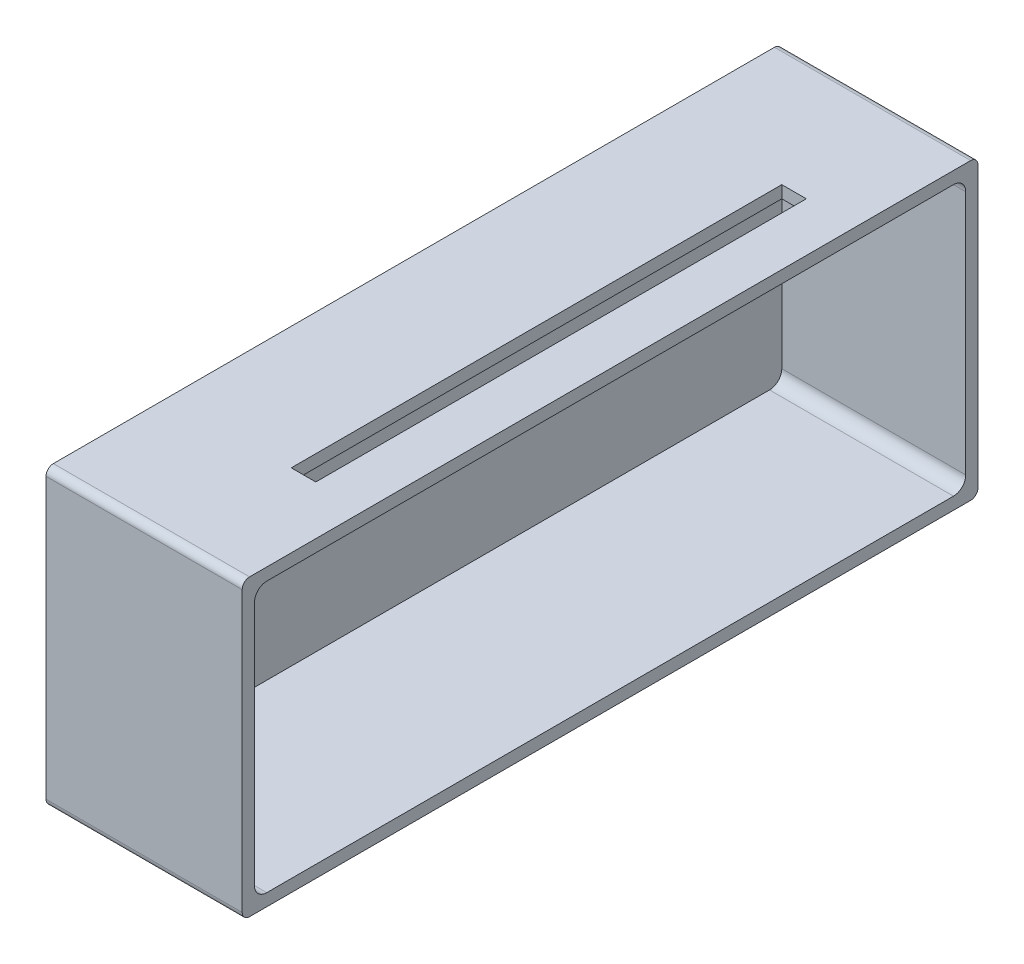
SolidWorks part; units mm, degrees
material "1060 合金"
ref_plane "前视基准面" through (0, 0, 0) normal (0, 0, 1) x (1, 0, 0)
ref_plane "上视基准面" through (0, 0, 0) normal (0, 1, 0) x (1, 0, 0)
ref_plane "右视基准面" through (0, 0, 0) normal (1, 0, 0) x (0, 0, -1)
other "Configuration Table"
sketch "草图1" plane through (0, 0, 0) normal (1, 0, 0) x (0, 0, -1)
  line L17 (-146.9915, 127.8502) -> (153.0085, 127.8502)
  line L18 (-146.9915, 127.8502) -> (-146.9915, 7.8502)
  line L19 (-146.9915, 7.8502) -> (153.0085, 7.8502)
  line L20 (153.0085, 127.8502) -> (153.0085, 7.8502)
  line L21 (-141.9915, 122.8502) -> (148.0085, 122.8502) construction
  line L22 (-141.9915, 122.8502) -> (-141.9915, 12.8502) construction
  line L23 (-141.9915, 12.8502) -> (148.0085, 12.8502) construction
  line L24 (148.0085, 122.8502) -> (148.0085, 12.8502) construction
  dimension "D1" = 300
  dimension "D2" = 120
  dimension "D3" = 290
  dimension "D4" = 5
  dimension "D5" = 110
  dimension "D6" = 5
extrude "凸台-拉伸1" add sketch "草图1" along normal blind 80
fillet "圆角1" radius 3 4 edges at (40, 7.8502, -153.0085) (40, 7.8502, 146.9915) (40, 127.8502, -153.0085) (40, 127.8502, 146.9915)
shell "抽壳1" thickness 5
fillet "圆角2" radius 5 4 edges at (42.5, 12.8502, 141.9915) (42.5, 12.8502, -148.0085) (42.5, 122.8502, -148.0085) (42.5, 122.8502, 141.9915)
sketch "草图3" plane through (0, 127.8502, 0) normal (0, 1, 0) x (1, 0, 0)
  line L0 (0, 153.0085) -> (80, 153.0085) construction
  line L1 (50, 103.0085) -> (60, 103.0085)
  line L2 (50, 103.0085) -> (50, -96.9915)
  line L3 (50, -96.9915) -> (60, -96.9915)
  line L4 (60, 103.0085) -> (60, -96.9915)
  line L5 (0, 150.0085) -> (0, -143.9915) construction
  dimension "D1" = 200
  dimension "D2" = 50
  dimension "D3" = 10
  dimension "D4" = 50
extrude "切除-拉伸1" cut sketch "草图3" against normal blind 5
